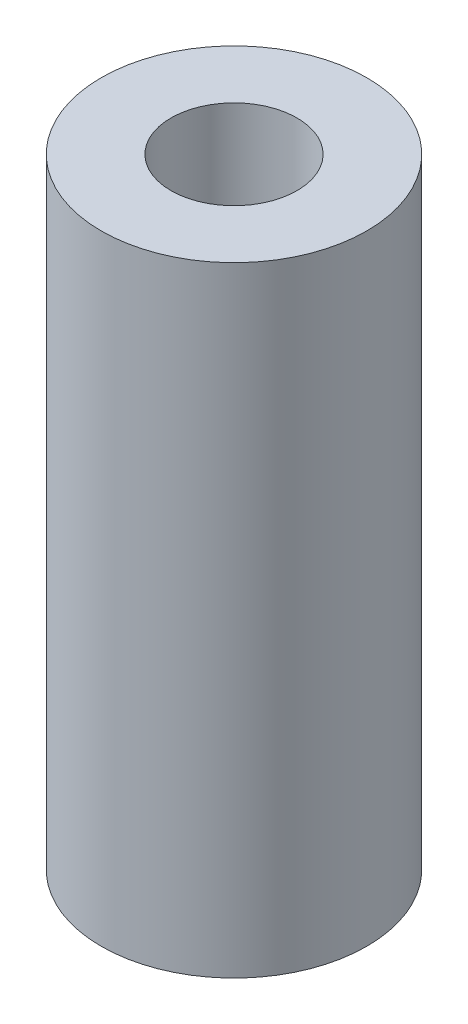
SolidWorks part; units mm, degrees
ref_plane "Front Plane" through (0, 0, 0) normal (0, 0, 1) x (1, 0, 0)
ref_plane "Top Plane" through (0, 0, 0) normal (0, 1, 0) x (1, 0, 0)
ref_plane "Right Plane" through (0, 0, 0) normal (1, 0, 0) x (0, 0, -1)
sketch "Sketch1" plane through (0, 0, 0) normal (0, 1, 0) x (1, 0, 0)
  circle A0 centre (0, 0) radius 2.3813
  dimension "D1" = 4.7625
extrude "Boss-Extrude1" add sketch "Sketch1" along normal blind 11.1125
hole_wizard "Tap Drill for #4-40 Tap1" positions "Sketch7" profile "Sketch6" hole size "#4-40" standard "Ansi Inch" end condition up to next
sketch "Sketch7" plane through (0, 11.1125, 0) normal (0, 1, 0) x (-1, 0, 0)
  circle A0 centre (0, 0) radius 2.3813 construction
  point P0 (0, 0)
sketch "Sketch6" plane through (0, 11.1125, 0) normal (1, 0, 0) x (0, 0, 1)
  line L0 (0, 0) -> (0, 11.1125)
  line L1 (0, 11.1125) -> (1.1303, 11.1125)
  line L2 (1.1303, 11.1125) -> (1.1303, 0)
  line L5 (1.1303, 0) -> (0, 0)
  line L11 (0, -6.35) -> (0, 107.95) construction
  dimension "Thru Hole Dia." = 2.2606
  dimension "Thru Hole Depth" = 11.1125
